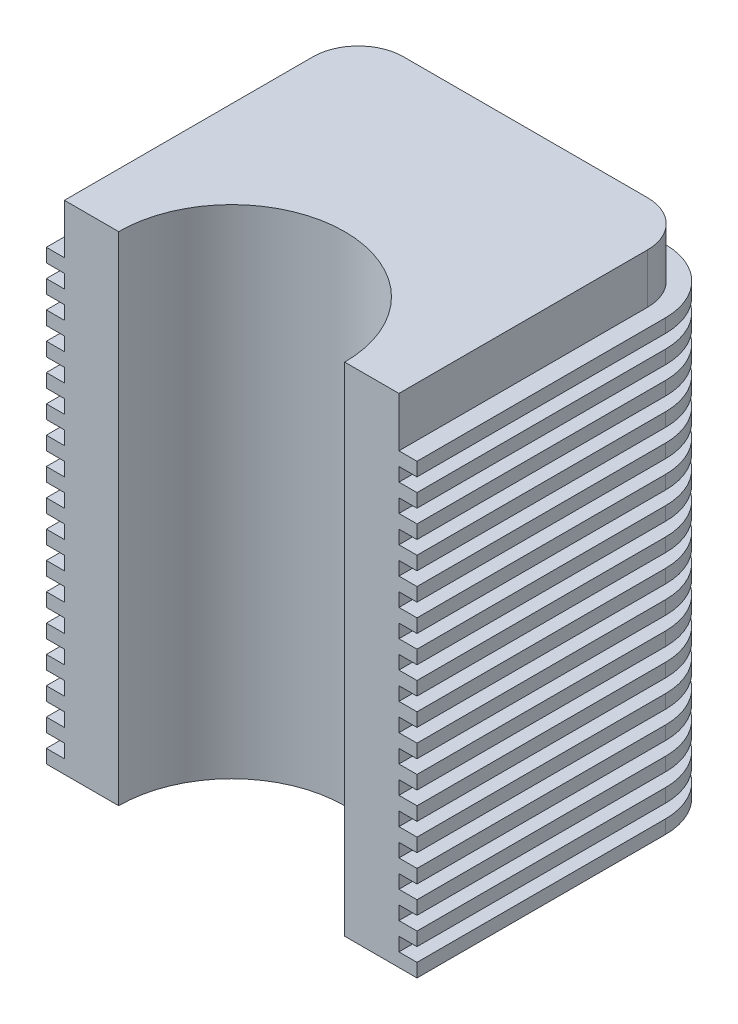
SolidWorks part; units mm, degrees
ref_plane "Front Plane" through (0, 0, 0) normal (0, 0, 1) x (1, 0, 0)
ref_plane "Top Plane" through (0, 0, 0) normal (0, 1, 0) x (1, 0, 0)
ref_plane "Right Plane" through (0, 0, 0) normal (1, 0, 0) x (0, 0, -1)
sketch "Sketch2" plane through (0, 0, 0) normal (0, 1, 0) x (1, 0, 0)
  line L0 (25, 0) -> (37, 0)
  line L1 (37, 0) -> (37, 55)
  line L2 (27, 65) -> (-27, 65)
  line L3 (0, 0) -> (0, 57.5745) construction
  line L4 (-25, 0) -> (-37, 0)
  line L5 (-37, 0) -> (-37, 55)
  arc A0 (25, 0) -> (-25, 0) centre (0, 0) ccw
  arc A1 (37, 55) -> (27, 65) centre (27, 55) ccw
  arc A2 (-37, 55) -> (-27, 65) centre (-27, 55) cw
  point P11 (0, 65)
  point P13 (37, 65)
  point P16 (-37, 65)
  dimension "D1" = 50
  dimension "D4" = 10
  dimension "D2" = 12
  dimension "D3" = 65
extrude "Boss-Extrude1" add sketch "Sketch2" along normal blind 110
sketch "Sketch3" plane through (0, 0, 0) normal (0, -1, 0) x (1, 0, 0)
  line L1 (41, -55) -> (41, 0)
  line L2 (-27, -69) -> (27, -69)
  line L3 (-41, 0) -> (-41, -55)
  line L5 (-25, 0) -> (-37, 0)
  line L6 (-37, 0) -> (-37, -55)
  line L7 (-27, -65) -> (27, -65)
  line L8 (37, -55) -> (37, 0)
  line L9 (37, 0) -> (25, 0)
  line L10 (-25, 0) -> (-37, 0)
  line L11 (-37, 0) -> (-37, -55)
  line L12 (-27, -65) -> (27, -65)
  line L13 (37, -55) -> (37, 0)
  line L14 (37, 0) -> (25, 0)
  line L15 (-37, 0) -> (-41, 0)
  line L16 (37, 0) -> (41, 0)
  line L18 (-41, 4) -> (-41, -55) construction
  line L19 (-20.6155, 4) -> (-41, 4) construction
  line L20 (41, 4) -> (20.6155, 4) construction
  line L21 (41, -55) -> (41, 4) construction
  arc A1 (27, -69) -> (41, -55) centre (27, -55) ccw
  arc A2 (-41, -55) -> (-27, -69) centre (-27, -55) ccw
  arc A3 (-25, 0) -> (25, 0) centre (0, 0) ccw
  arc A4 (-37, -55) -> (-27, -65) centre (-27, -55) ccw
  arc A5 (27, -65) -> (37, -55) centre (27, -55) ccw
  arc A6 (-25, 0) -> (25, 0) centre (0, 0) ccw
  arc A7 (-37, -55) -> (-27, -65) centre (-27, -55) ccw
  arc A8 (27, -65) -> (37, -55) centre (27, -55) ccw
  arc A9 (-20.6155, 4) -> (20.6155, 4) centre (0, 0) ccw construction
  line M19 (-37, 0) -> (-37, -55)
  arc M20 (-37, -55) -> (-27, -65) centre (-27, -55) ccw
  line M21 (-27, -65) -> (27, -65)
  arc M22 (27, -65) -> (37, -55) centre (27, -55) ccw
  line M23 (37, -55) -> (37, 0)
  dimension "D1" = 0
  dimension "D2" = 4
extrude "Boss-Extrude2" add sketch "Sketch3" against normal blind 3 contours L3 A2 L2 A1 L1 L16 L15 M23 M22 M21 M20 M19
pattern_linear "LPattern2" count 17 spacing 6 along (0, 1, 0) of "Boss-Extrude2"
